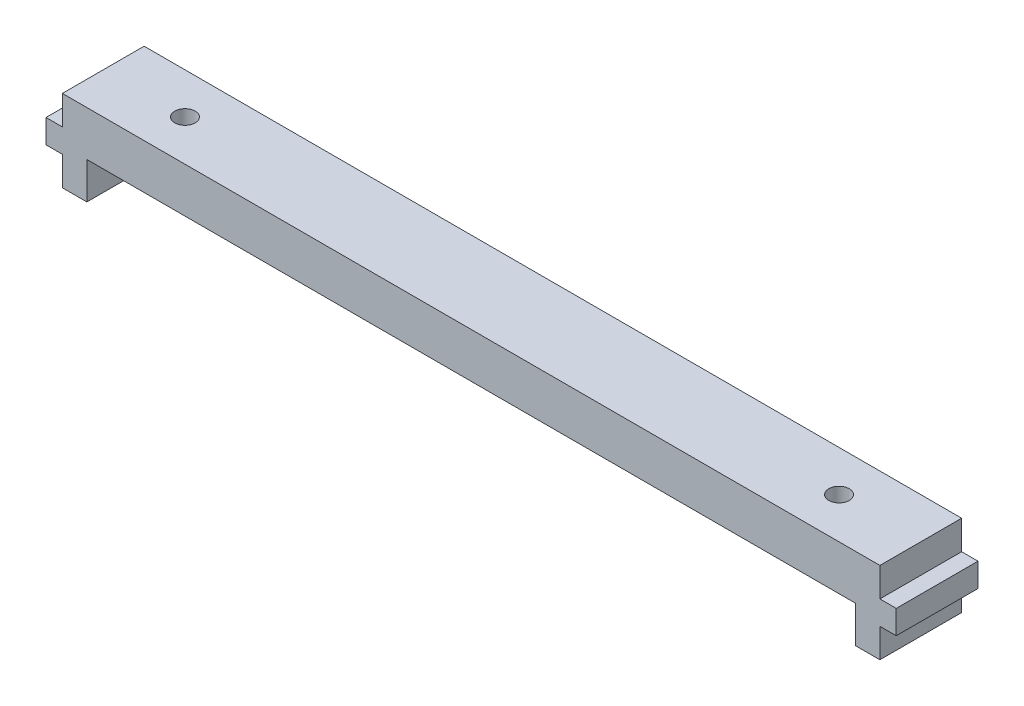
SolidWorks part; units mm, degrees
ref_plane "Front Plane" through (0, 0, 0) normal (0, 0, 1) x (1, 0, 0)
ref_plane "Top Plane" through (0, 0, 0) normal (0, 1, 0) x (1, 0, 0)
ref_plane "Right Plane" through (0, 0, 0) normal (1, 0, 0) x (0, 0, -1)
sketch "Sketch1" plane through (0, 0, 0) normal (0, 0, 1) x (1, 0, 0)
  line L0 (-50, 5.5) -> (-50, 1.95)
  line L1 (-50, 1.95) -> (-52, 1.95)
  line L2 (-52, 1.95) -> (-52, -0.95)
  line L3 (-52, -0.95) -> (-50, -0.95)
  line L4 (-50, -0.95) -> (-50, -4.5)
  line L5 (-50, -4.5) -> (-47, -4.5)
  line L6 (-47, -4.5) -> (-47, 0)
  line L7 (-47, 0) -> (0, 0)
  line L8 (-50, 5.5) -> (0, 5.5)
  line L9 (0, 5.5) -> (0, 0)
  dimension "D1" = 3
  dimension "D2" = 50
  dimension "D3" = 2
  dimension "D4" = 2.9
  dimension "D5" = 4.5
  dimension "D6" = 10
extrude "MainLeft" add sketch "Sketch1" along normal blind 10
sketch "Sketch3" plane through (0, 0, 0) normal (0, -1, 0) x (1, 0, 0)
  line L0 (0, 10) -> (0, 0) construction
  circle A0 centre (-40, 5) radius 1.25
  point P5 (0, 5)
  dimension "D1" = 40
  dimension "D2" = 2.5
extrude "Cut-Extrude2" cut sketch "Sketch3" against normal through all
mirror "Mirror1" about plane through (0, 0, 0) normal (1, 0, 0) of "MainLeft", "Cut-Extrude2"
